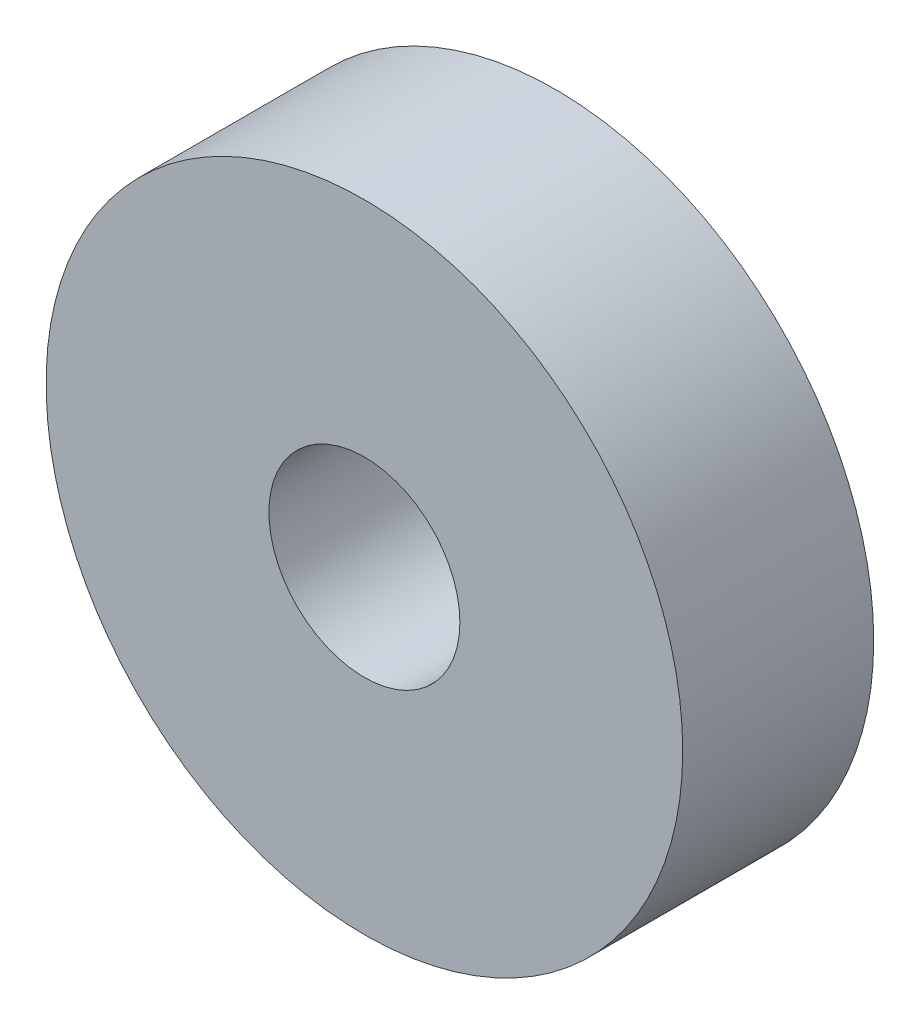
SolidWorks part; units mm, degrees
ref_plane "Plan de face" through (0, 0, 0) normal (0, 0, 1) x (1, 0, 0)
ref_plane "Plan de dessus" through (0, 0, 0) normal (0, 1, 0) x (1, 0, 0)
ref_plane "Plan de droite" through (0, 0, 0) normal (1, 0, 0) x (0, 0, -1)
sketch "Esquisse3" plane through (0, 0, 0) normal (0, 0, 1) x (1, 0, 0)
  circle A0 centre (8.9312, 26.4578) radius 1.5
  circle A1 centre (8.9312, 26.4578) radius 5
  dimension "D1" = 10
  dimension "D2" = 3
extrude "Boss.-Extru.3" add sketch "Esquisse3" along normal blind 3 separate body
